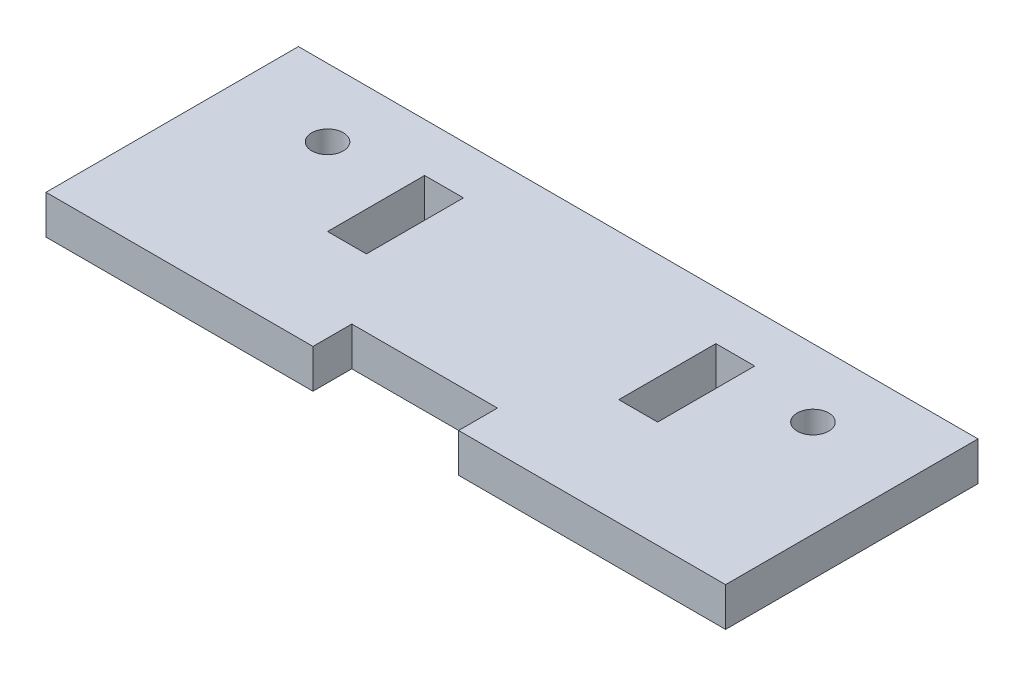
SolidWorks part; units mm, degrees
ref_plane "Front Plane" through (0, 0, 0) normal (0, 0, 1) x (1, 0, 0)
ref_plane "Top Plane" through (0, 0, 0) normal (0, 1, 0) x (1, 0, 0)
ref_plane "Right Plane" through (0, 0, 0) normal (1, 0, 0) x (0, 0, -1)
sketch "Sketch1" plane through (0, 0, 0) normal (0, 1, 0) x (1, 0, 0)
  line L0 (20, 26) -> (20, 0) construction
  line L1 (0, 0) -> (20, 0)
  line L2 (0, 0) -> (0, 26)
  line L3 (0, 26) -> (70, 26)
  line L4 (70, 0) -> (70, 26)
  line L5 (50, 26) -> (50, 0) construction
  line L6 (35, 26) -> (35, 4) construction
  line L7 (18, 21) -> (22, 21)
  line L8 (18, 21) -> (18, 11)
  line L9 (18, 11) -> (22, 11)
  line L10 (22, 21) -> (22, 11)
  line L11 (52, 11) -> (48, 11)
  line L12 (48, 21) -> (48, 11)
  line L13 (52, 21) -> (52, 11)
  line L14 (52, 21) -> (48, 21)
  line L15 (20, 0) -> (27.5, 0)
  line L17 (27.5, 0) -> (27.5, 26) construction
  line L26 (50, 0) -> (70, 0)
  line L27 (42.5, 0) -> (50, 0)
  line L30 (27.5, 0) -> (27.5, 4)
  line L31 (27.5, 4) -> (42.5, 4)
  line L32 (42.5, 0) -> (42.5, 4)
  circle A0 centre (10, 19) radius 1.625
  circle A2 centre (60, 19) radius 1.625
  dimension "D10" = 7.5
  dimension "D11" = 4
  dimension "D13" = 3.25
  dimension "D1" = 70
  dimension "D2" = 26
  dimension "D3" = 20
  dimension "D4" = 10
  dimension "D5" = 4
  dimension "D6" = 10
  dimension "D7" = 2
  dimension "D8" = 5
  dimension "D9" = 7
extrude "Boss-Extrude1" add sketch "Sketch1" along normal blind 4
